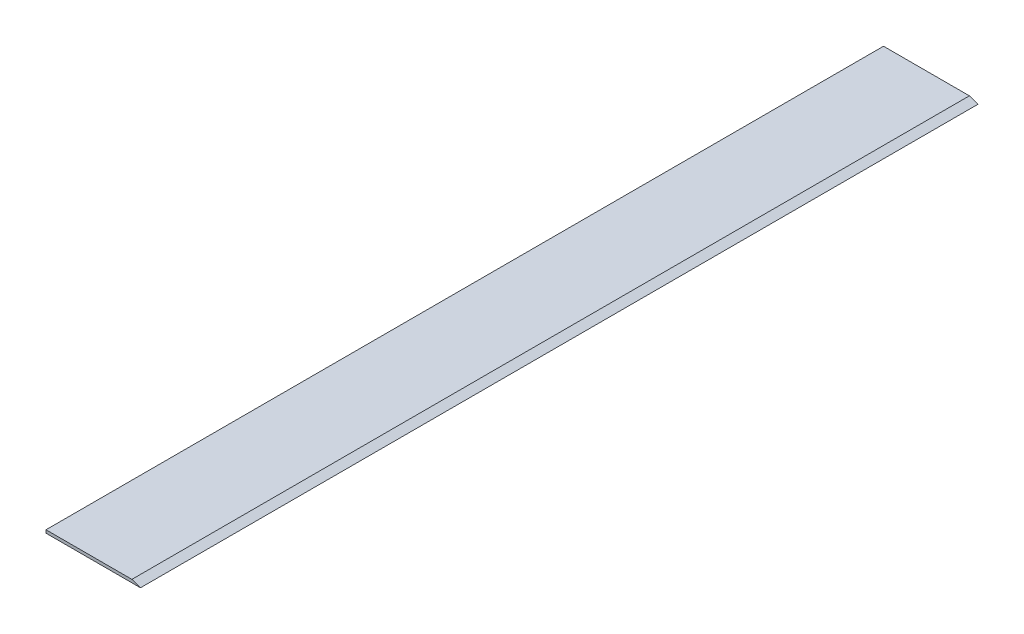
SolidWorks part; units mm, degrees
ref_plane "Alzado" through (0, 0, 0) normal (0, 0, 1) x (1, 0, 0)
ref_plane "Planta" through (0, 0, 0) normal (0, 1, 0) x (1, 0, 0)
ref_plane "Vista lateral" through (0, 0, 0) normal (1, 0, 0) x (0, 0, -1)
sketch "Croquis1" plane through (0, 0, 0) normal (0, 0, 1) x (1, 0, 0)
  line L0 (0, 0) -> (22, 0)
  line L1 (22, 0) -> (20, 0.7)
  line L2 (20, 0.7) -> (0, 0.7)
  line L3 (0, 0.7) -> (0, 0)
  dimension "D1" = 0.7
  dimension "D2" = 22
  dimension "D3" = 2
  dimension "D4" = 19.29
extrude "Saliente-Extruir1" add sketch "Croquis1" along normal blind 195
